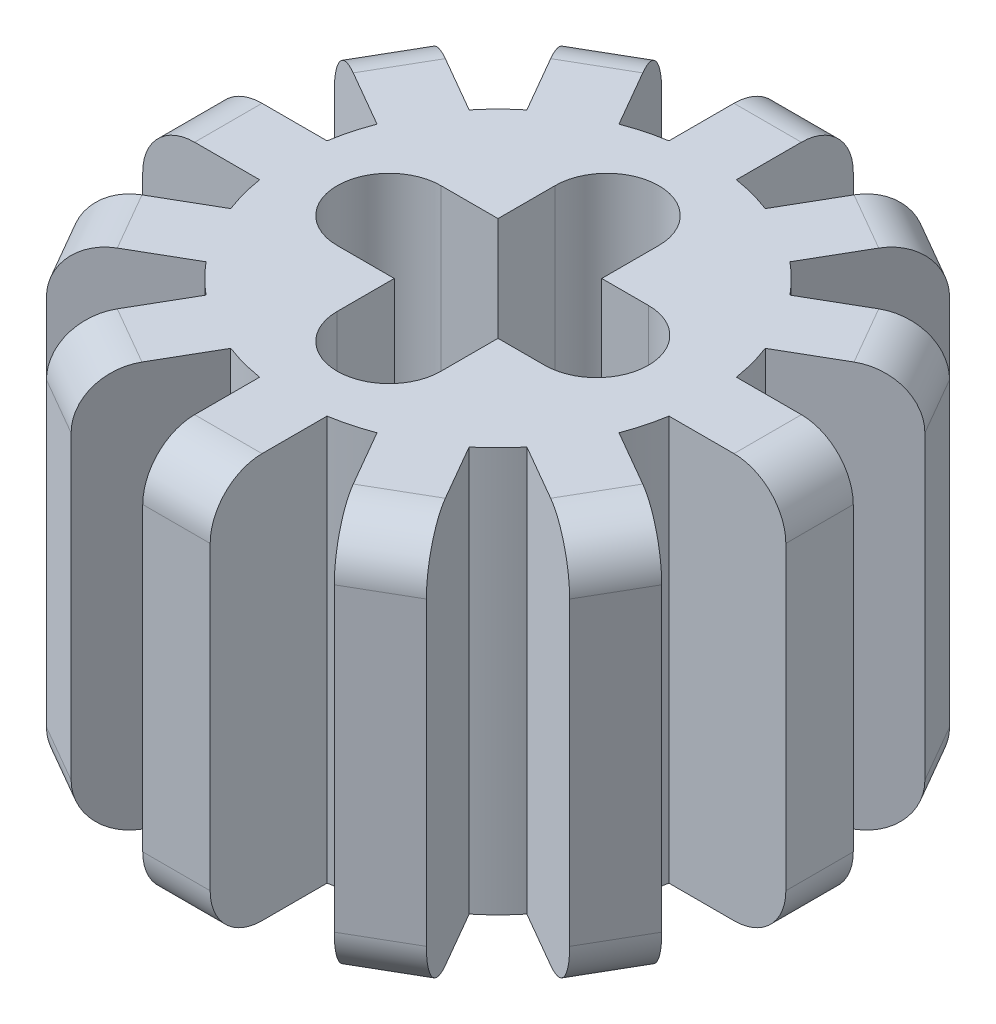
SolidWorks part; units mm, degrees
ref_plane "Front Plane" through (0, 0, 0) normal (0, 0, 1) x (1, 0, 0)
ref_plane "Top Plane" through (0, 0, 0) normal (0, 1, 0) x (1, 0, 0)
ref_plane "Right Plane" through (0, 0, 0) normal (1, 0, 0) x (0, 0, -1)
sketch "Sketch1" plane through (0, 0, 0) normal (0, 1, 0) x (1, 0, 0)
  circle A1 centre (0, 0) radius 4
  dimension "D1" = 8
extrude "Boss-Extrude1" add sketch "Sketch1" along normal mid plane 7.8
sketch "Sketch2" plane through (0, 3.9, 0) normal (0, 1, 0) x (1, 0, 0)
  line L0 (0, 0) -> (0, 50000) construction
  line L1 (0, 0) -> (50000, 0) construction
  line L2 (0, 4) -> (0, 1.5) construction
  line L3 (0, -4) -> (0, -1.5) construction
  line L4 (-4, 0) -> (-1.5, 0) construction
  line L5 (4, 0) -> (1.5, 0) construction
  line L6 (0, 0) -> (0, 4) construction
  line L13 (0, 1.5) -> (0.65, 1.5) construction
  line L16 (0, 1.5) -> (-0.65, 1.5) construction
  circle A1 centre (0, 0) radius 4 construction
  dimension "D1" = 2.5
  dimension "D2" = 2.5
  dimension "D3" = 2.5
  dimension "D4" = 2.5
sketch "Sketch5" plane through (0, 3.9, 0) normal (0, 1, 0) x (1, 0, 0)
  line L0 (0, 0) -> (0, 4) construction
  line L1 (0, 4) -> (0, 6.2)
  line L2 (0, 6.2) -> (-0.65, 6.2)
  line L3 (0, 6.2) -> (0.65, 6.2)
  line L4 (-0.65, 6.2) -> (-0.65, 3.9468)
  line L5 (0.65, 6.2) -> (0.65, 3.9468)
  line L6 (-0.65, 3.9468) -> (0.65, 3.9468)
  circle A0 centre (0, 0) radius 4 construction
  circle M4 centre (0, 0) radius 4
extrude "Boss-Extrude2" add sketch "Sketch5" against normal blind 7.8 contours L2 L4 L1 M4 | L5 L3 L1 M4
sketch "Sketch6" plane through (0, 3.9, 0) normal (0, 1, 0) x (1, 0, 0)
  circle A0 centre (0, 0) radius 4 construction
pattern_circular "CirPattern1" count 12 over 360 about axis through (0, 0, 0) along (0, 1, 0) of "Boss-Extrude2"
sketch "Sketch7" plane through (0, 3.9, 0) normal (0, 1, 0) x (1, 0, 0)
  line L0 (0, 0) -> (0, -2.1) construction
  line L1 (0, 0) -> (0, 2.1) construction
  line L2 (0, 2.1) -> (0, -2.1) construction
  line L3 (1, 2.1) -> (1, -2.1)
  line L4 (-1, 2.1) -> (-1, -2.1)
  line L5 (0, 0) -> (-2.1, 0) construction
  line L6 (0, 0) -> (1.9, 0) construction
  line L7 (-2.1, 0) -> (1.9, 0) construction
  line L8 (-2.1, 1) -> (1.9, 1)
  line L9 (-2.1, -1) -> (1.9, -1)
  arc A0 (1, 2.1) -> (-1, 2.1) centre (0, 2.1) ccw
  arc A1 (-1, -2.1) -> (1, -2.1) centre (0, -2.1) ccw
  arc A2 (-2.1, 1) -> (-2.1, -1) centre (-2.1, 0) ccw
  arc A3 (1.9, -1) -> (1.9, 1) centre (1.9, 0) ccw
  point P3 (0, 0)
  point P9 (-0.1, 0)
  dimension "D3" = 2.1
  dimension "D1" = 2.1
  dimension "D2" = 2.1
extrude "Cut-Extrude2" cut sketch "Sketch7" against normal through all contours L3 A0 L4 L8 | L4 L9 L3 L8 | L9 A3 L8 L3 | L4 A1 L3 L9 | L8 A2 L9 L4
fillet "Fillet4" radius 1 1 edges at (3.1, 3.9, -5.3694)
fillet "Fillet5" radius 1 1 edges at (5.3694, 3.9, 3.1)
fillet "Fillet6" radius 1 1 edges at (6.2, 3.9, 0)
fillet "Fillet7" radius 1 1 edges at (5.3694, -3.9, -3.1)
fillet "Fillet8" radius 1 1 edges at (3.1, -3.9, 5.3694)
fillet "Fillet9" radius 1 1 edges at (3.1, 3.9, 5.3694)
fillet "Fillet10" radius 1 1 edges at (0, 3.9, 6.2)
fillet "Fillet11" radius 1 1 edges at (-3.1, 3.9, 5.3694)
fillet "Fillet12" radius 1 1 edges at (-5.3694, 3.9, 3.1)
fillet "Fillet13" radius 1 1 edges at (-6.2, 3.9, 0)
fillet "Fillet14" radius 1 1 edges at (-3.1, 3.9, -5.3694)
fillet "Fillet15" radius 1 1 edges at (-5.3694, 3.9, -3.1)
fillet "Fillet16" radius 1 1 edges at (0, 3.9, -6.2)
fillet "Fillet17" radius 1 1 edges at (5.3694, 3.9, -3.1)
fillet "Fillet18" radius 1 1 edges at (-6.2, -3.9, 0)
fillet "Fillet19" radius 1 1 edges at (-5.3694, -3.9, 3.1)
fillet "Fillet20" radius 1 1 edges at (-3.1, -3.9, 5.3694)
fillet "Fillet21" radius 1 1 edges at (0, -3.9, 6.2)
fillet "Fillet22" radius 1 1 edges at (5.3694, -3.9, 3.1)
fillet "Fillet23" radius 1 1 edges at (6.2, -3.9, 0)
fillet "Fillet24" radius 1 1 edges at (0, -3.9, -6.2)
fillet "Fillet25" radius 1 1 edges at (-3.1, -3.9, -5.3694)
fillet "Fillet26" radius 1 1 edges at (3.1, -3.9, -5.3694)
fillet "Fillet27" radius 1 1 edges at (-5.3694, -3.9, -3.1)
